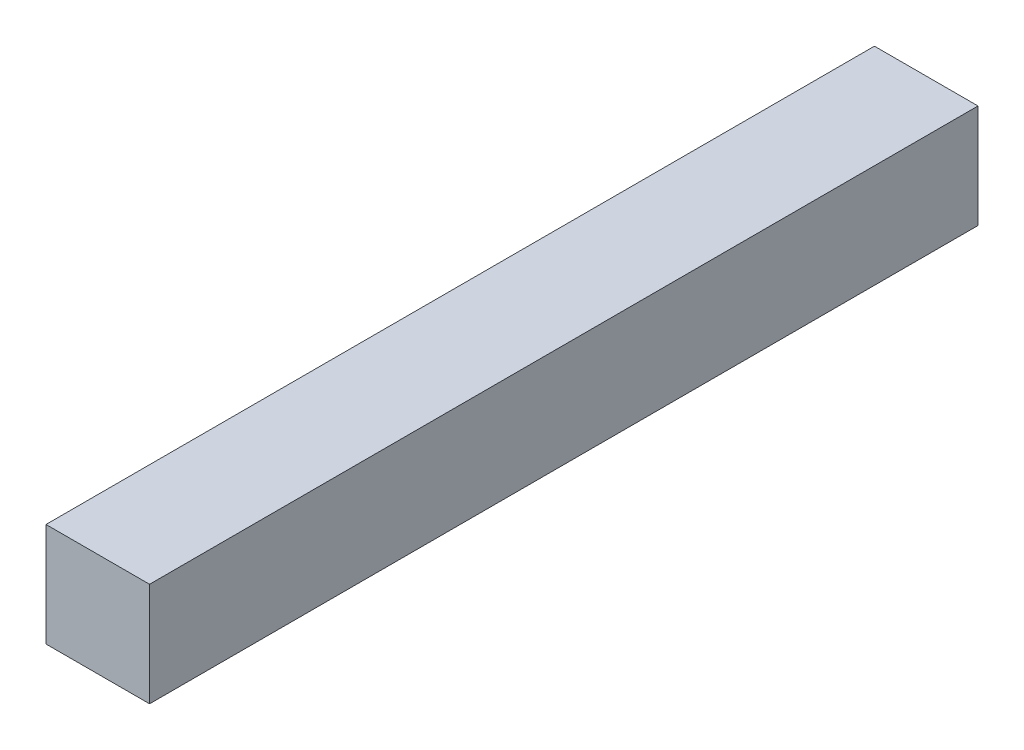
SolidWorks part; units mm, degrees
ref_plane "Alzado" through (0, 0, 0) normal (0, 0, 1) x (1, 0, 0)
ref_plane "Planta" through (0, 0, 0) normal (0, 1, 0) x (1, 0, 0)
ref_plane "Vista lateral" through (0, 0, 0) normal (1, 0, 0) x (0, 0, -1)
sketch "Croquis1" plane through (0, 0, 0) normal (0, 0, 1) x (1, 0, 0)
  line L1 (-20.4403, 22.956) -> (29.5597, 22.956)
  line L2 (-20.4403, 22.956) -> (-20.4403, -27.044)
  line L3 (-20.4403, -27.044) -> (29.5597, -27.044)
  line L4 (29.5597, 22.956) -> (29.5597, -27.044)
  dimension "D1" = 50
  dimension "D2" = 50
extrude "Saliente-Extruir1" add sketch "Croquis1" along normal blind 400
